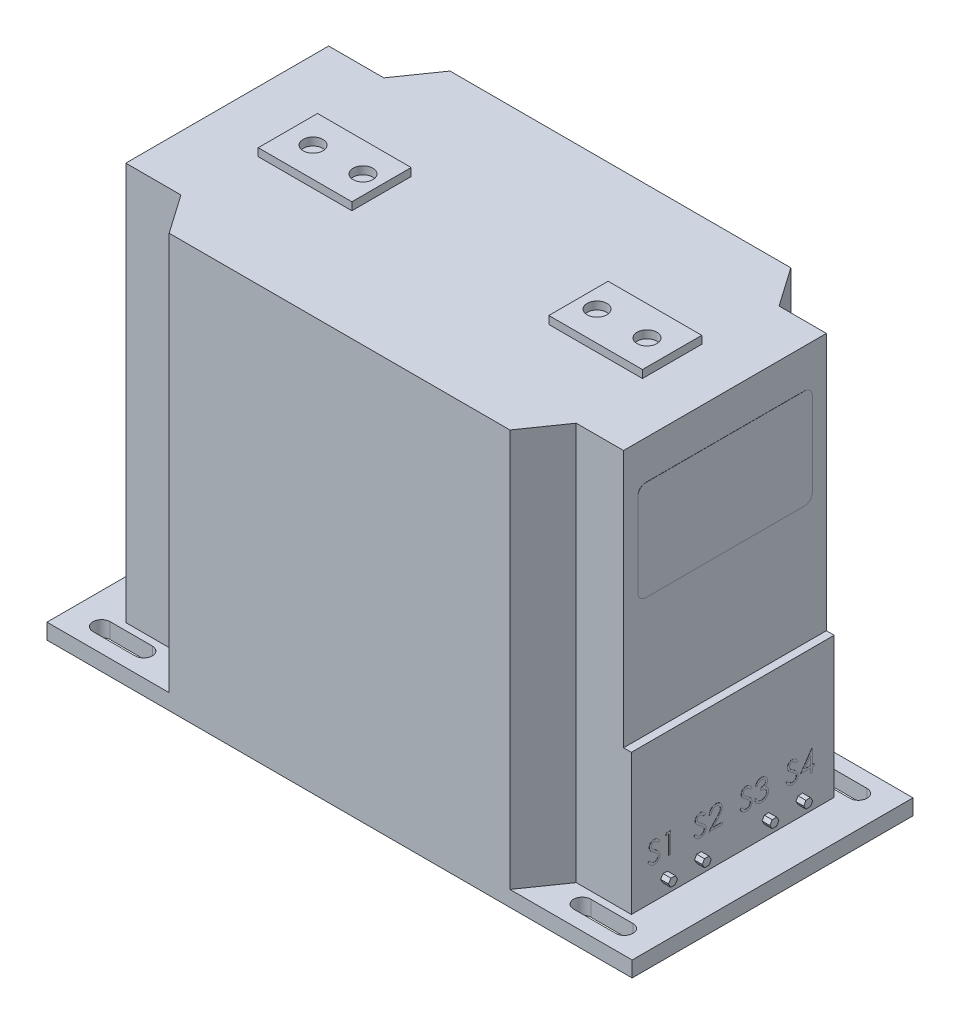
SolidWorks part; units mm, degrees
ref_plane "Alzado" through (0, 0, 0) normal (0, 0, 1) x (1, 0, 0)
ref_plane "Planta" through (0, 0, 0) normal (0, 1, 0) x (1, 0, 0)
ref_plane "Vista lateral" through (0, 0, 0) normal (1, 0, 0) x (0, 0, -1)
sketch "Croquis1" plane through (0, 0, 0) normal (0, 1, 0) x (1, 0, 0)
  line L1 (-187.5, 90) -> (187.5, 90)
  line L2 (-187.5, 90) -> (-187.5, -90)
  line L3 (-187.5, -90) -> (187.5, -90)
  line L4 (187.5, 90) -> (187.5, -90)
  line L5 (-187.5, 90) -> (187.5, -90) construction
  line L6 (-187.5, -90) -> (187.5, 90) construction
  point P0 (0, 0)
  dimension "D1" = 375
  dimension "D2" = 180
extrude "Saliente-Extruir1" add sketch "Croquis1" along normal blind 265
sketch "Croquis2" plane through (0, 265, 0) normal (0, 1, 0) x (1, 0, 0)
  line L0 (0, 0) -> (75, 0) construction
  line L1 (75, 0) -> (107, 0) construction
  line L2 (63.1078, 19) -> (63.1078, -19)
  line L3 (63.1078, -19) -> (123.1078, -19)
  line L4 (123.1078, -19) -> (123.1078, 19)
  line L5 (123.1078, 19) -> (63.1078, 19)
  line L6 (0, 0) -> (0, -29.2326) construction
  line L7 (-75, 0) -> (-107, 0) construction
  line L8 (-123.1078, 19) -> (-63.1078, 19)
  line L9 (-123.1078, -19) -> (-123.1078, 19)
  line L10 (-63.1078, -19) -> (-123.1078, -19)
  line L11 (-63.1078, 19) -> (-63.1078, -19)
  circle A0 centre (75, 0) radius 6.35
  circle A1 centre (107, 0) radius 6.35
  circle A2 centre (-107, 0) radius 6.35
  circle A3 centre (-75, 0) radius 6.35
  dimension "D2" = 12.7
  dimension "D3" = 12.7
  dimension "D1" = 75
  dimension "D4" = 32
  dimension "D5" = 38
  dimension "D6" = 60
  dimension "D7" = 19
extrude "Saliente-Extruir2" add sketch "Croquis2" along normal blind 5
sketch "Croquis3" plane through (0, 265, 0) normal (0, 1, 0) x (1, 0, 0)
  line L0 (0, 0) -> (0, 90) construction
  line L1 (187.5, 90) -> (-187.5, 90) construction
  line L2 (167.5, 75) -> (140.5, 75) construction
  line L3 (167.5, 69.5) -> (140.5, 69.5)
  line L4 (167.5, 80.5) -> (140.5, 80.5)
  line L5 (0, 0) -> (187.5, 0) construction
  line L6 (187.5, -90) -> (187.5, 90) construction
  line L7 (-167.5, 75) -> (-140.5, 75) construction
  line L8 (-167.5, 69.5) -> (-140.5, 69.5)
  line L9 (-167.5, 80.5) -> (-140.5, 80.5)
  line L10 (-167.5, -75) -> (-140.5, -75) construction
  line L11 (-167.5, -69.5) -> (-140.5, -69.5)
  line L12 (-167.5, -80.5) -> (-140.5, -80.5)
  line L13 (167.5, -75) -> (140.5, -75) construction
  line L14 (167.5, -69.5) -> (140.5, -69.5)
  line L15 (167.5, -80.5) -> (140.5, -80.5)
  line L16 (-126.6467, 65) -> (-109.1945, 90)
  line L17 (-162, 65) -> (-126.6467, 65)
  line L18 (-162, 65) -> (-162, -65)
  line L19 (-162, -65) -> (-126.6467, -65)
  line L20 (162, 65) -> (162, -65)
  line L21 (-162, 65) -> (162, -65) construction
  line L22 (-162, -65) -> (162, 65) construction
  line L23 (-126.6467, -65) -> (-109.1945, -90)
  line L24 (-187.5, -90) -> (187.5, -90) construction
  line L25 (126.6467, -65) -> (109.1945, -90)
  line L26 (126.6467, 65) -> (109.1945, 90)
  line L27 (126.6467, 65) -> (162, 65)
  line L28 (126.6467, -65) -> (162, -65)
  arc A0 (167.5, 69.5) -> (167.5, 80.5) centre (167.5, 75) ccw
  arc A1 (140.5, 80.5) -> (140.5, 69.5) centre (140.5, 75) ccw
  arc A2 (-167.5, 69.5) -> (-167.5, 80.5) centre (-167.5, 75) cw
  arc A3 (-140.5, 80.5) -> (-140.5, 69.5) centre (-140.5, 75) cw
  arc A4 (-167.5, -69.5) -> (-167.5, -80.5) centre (-167.5, -75) ccw
  arc A5 (-140.5, -80.5) -> (-140.5, -69.5) centre (-140.5, -75) ccw
  arc A6 (167.5, -69.5) -> (167.5, -80.5) centre (167.5, -75) cw
  arc A7 (140.5, -80.5) -> (140.5, -69.5) centre (140.5, -75) cw
  point P7 (154, 75)
  point P17 (-154, 75)
  point P24 (-154, -75)
  point P31 (154, -75)
  point P46 (-117.9206, -77.5)
  line M16 (187.5, -90) -> (187.5, 90)
  line M17 (187.5, 90) -> (-187.5, 90)
  line M18 (-187.5, 90) -> (-187.5, -90)
  line M19 (-187.5, -90) -> (187.5, -90)
  dimension "D1" = 75
  dimension "D2" = 167.5
  dimension "D3" = 27
  dimension "D4" = 11
  dimension "D5" = 162
  dimension "D6" = 130
extrude "Cortar-Extruir1" cut sketch "Croquis3" against normal blind 255 contours L23 L19 L18 L17 L16 A5 L12 A4 L11 L9 A3 L8 A2 M17 M18 M19 | L28 L25 L26 L27 L20 A1 L4 A0 L3 L15 A7 L14 A6 M19 M16 M17
sketch "Croquis4" plane through (0, 265, 0) normal (0, 1, 0) x (1, 0, 0)
  line L0 (-167.5, 75) -> (-140.5, 75) construction
  line L1 (-167.5, 80.5) -> (-140.5, 80.5)
  line L2 (-167.5, 69.5) -> (-140.5, 69.5)
  line L3 (-167.5, -75) -> (-140.5, -75) construction
  line L4 (-167.5, -69.5) -> (-140.5, -69.5)
  line L5 (-167.5, -80.5) -> (-140.5, -80.5)
  line L6 (140.5, 75) -> (167.5, 75) construction
  line L7 (140.5, 80.5) -> (167.5, 80.5)
  line L8 (140.5, 69.5) -> (167.5, 69.5)
  line L9 (140.5, -75) -> (167.5, -75) construction
  line L10 (140.5, -69.5) -> (167.5, -69.5)
  line L11 (140.5, -80.5) -> (167.5, -80.5)
  arc A0 (-167.5, 80.5) -> (-167.5, 69.5) centre (-167.5, 75) ccw
  arc A1 (-140.5, 69.5) -> (-140.5, 80.5) centre (-140.5, 75) ccw
  arc A2 (-167.5, -69.5) -> (-167.5, -80.5) centre (-167.5, -75) ccw
  arc A3 (-140.5, -80.5) -> (-140.5, -69.5) centre (-140.5, -75) ccw
  arc A4 (140.5, 80.5) -> (140.5, 69.5) centre (140.5, 75) ccw
  arc A5 (167.5, 69.5) -> (167.5, 80.5) centre (167.5, 75) ccw
  arc A6 (140.5, -69.5) -> (140.5, -80.5) centre (140.5, -75) ccw
  arc A7 (167.5, -80.5) -> (167.5, -69.5) centre (167.5, -75) ccw
  point P4 (-154, 75)
  point P13 (-154, -75)
  point P22 (154, 75)
  point P31 (154, -75)
  dimension "D1" = 11
  dimension "D2" = 11
  dimension "D3" = 11
  dimension "D4" = 11
extrude "Cortar-Extruir2" cut sketch "Croquis4" against normal blind 277
sketch "Croquis5" plane through (162, 0, 0) normal (1, 0, 0) x (0, 0, -1)
  line L0 (-65, 10) -> (-65, 100)
  line L1 (-65, 10) -> (-65, 265) construction
  line L2 (-65, 100) -> (65, 100)
  line L3 (65, 10) -> (65, 265) construction
  line L4 (65, 100) -> (65, 10)
  line L5 (65, 10) -> (-65, 10)
  line L6 (-65, 100) -> (-65, 265)
  line L7 (-65, 265) -> (65, 265)
  line L8 (65, 265) -> (65, 100)
  line M3 (65, 265) -> (-65, 265)
  line M4 (-65, 265) -> (-65, 10)
  line M6 (65, 10) -> (65, 265)
  dimension "D1" = 90
extrude "Cortar-Extruir3" cut sketch "Croquis5" against normal blind 5 contours L2 M4 M6 M3
sketch "Croquis6" plane through (162, 0, 0) normal (1, 0, 0) x (0, 0, -1)
  line L0 (0, 0) -> (0, 20) construction
  line L1 (0, 20) -> (21.6667, 20) construction
  line L3 (24.5534, 20) -> (23.11, 22.5)
  line L4 (23.11, 22.5) -> (20.2233, 22.5)
  line L5 (20.2233, 22.5) -> (18.7799, 20)
  line L6 (18.7799, 20) -> (20.2233, 17.5)
  line L7 (20.2233, 17.5) -> (23.11, 17.5)
  line L8 (23.11, 17.5) -> (24.5534, 20)
  line L9 (44.8571, 17.5461) -> (46.222, 20.0897)
  line L10 (46.222, 20.0897) -> (44.7016, 22.5437)
  line L11 (44.7016, 22.5437) -> (41.8163, 22.4539)
  line L12 (41.8163, 22.4539) -> (40.4513, 19.9103)
  line L13 (40.4513, 19.9103) -> (41.9717, 17.4563)
  line L14 (41.9717, 17.4563) -> (44.8571, 17.5461)
  line L15 (-41.9717, 17.4563) -> (-44.8571, 17.5461)
  line L16 (-40.4513, 19.9103) -> (-41.9717, 17.4563)
  line L17 (-41.8163, 22.4539) -> (-40.4513, 19.9103)
  line L18 (-44.7016, 22.5437) -> (-41.8163, 22.4539)
  line L19 (-46.222, 20.0897) -> (-44.7016, 22.5437)
  line L20 (-44.8571, 17.5461) -> (-46.222, 20.0897)
  line L21 (-23.11, 17.5) -> (-24.5534, 20)
  line L22 (-20.2233, 17.5) -> (-23.11, 17.5)
  line L23 (-18.7799, 20) -> (-20.2233, 17.5)
  line L24 (-20.2233, 22.5) -> (-18.7799, 20)
  line L25 (-23.11, 22.5) -> (-20.2233, 22.5)
  line L26 (-24.5534, 20) -> (-23.11, 22.5)
  circle A0 centre (21.6667, 20) radius 2.5 construction
  circle A1 centre (43.3367, 20) radius 2.5 construction
  circle A2 centre (-43.3367, 20) radius 2.5 construction
  circle A3 centre (-21.6667, 20) radius 2.5 construction
  dimension "D1" = 20
  dimension "D2" = 5
  dimension "D3" = 5
  dimension "D4" = 21.6667
  dimension "D5" = 21.67
extrude "Saliente-Extruir3" add sketch "Croquis6" along normal blind 5
sketch "Croquis7" plane through (162, 0, 0) normal (1, 0, 0) x (0, 0, -1)
  text T0 "\r\n\r\n\r\n  S1  S2  S3  S4" font "Century Gothic" height in points 50
extrude "Saliente-Extruir4" add sketch "Croquis7" along normal blind 0.1
sketch "Croquis8" plane through (157, 0, 0) normal (1, 0, 0) x (0, 0, -1)
  line L1 (-50.8517, 240.1495) -> (50.8517, 240.1495)
  line L2 (-55.8517, 235.1495) -> (-55.8517, 181.3189)
  line L3 (-50.8517, 176.3189) -> (50.8517, 176.3189)
  line L4 (55.8517, 235.1495) -> (55.8517, 181.3189)
  line L5 (-55.8517, 240.1495) -> (55.8517, 176.3189) construction
  line L6 (-55.8517, 176.3189) -> (55.8517, 240.1495) construction
  arc A0 (50.8517, 240.1495) -> (55.8517, 235.1495) centre (50.8517, 235.1495) cw
  arc A1 (50.8517, 176.3189) -> (55.8517, 181.3189) centre (50.8517, 181.3189) ccw
  arc A2 (-55.8517, 181.3189) -> (-50.8517, 176.3189) centre (-50.8517, 181.3189) ccw
  arc A3 (-50.8517, 240.1495) -> (-55.8517, 235.1495) centre (-50.8517, 235.1495) ccw
  point P0 (0, 208.2342)
  dimension "D1" = 5
extrude "Saliente-Extruir5" add sketch "Croquis8" along normal blind 0.1
sketch "Croquis9" plane through (-162, 0, 0) normal (-1, 0, 0) x (0, 0, 1)
  circle A0 centre (43.7616, 21.8867) radius 4.75
  point P2 (44.0014, 30.631)
  point P3 (43.7616, 21.8867)
  dimension "D1" = 9.5
extrude "Saliente-Extruir6" add sketch "Croquis9" along normal blind 5
